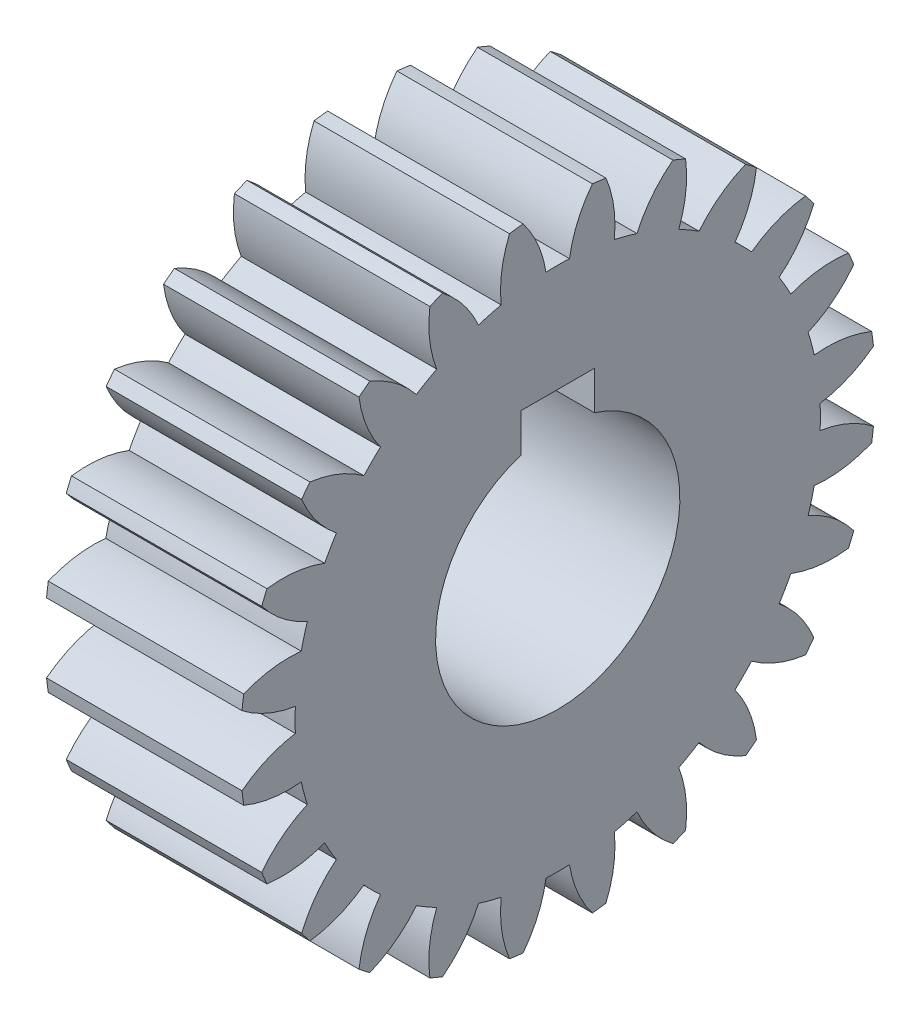
SolidWorks part; units mm, degrees
ref_plane "Plane1" through (0, 0, 0) normal (0, 0, 1) x (1, 0, 0)
ref_plane "Plane2" through (0, 0, 0) normal (0, 1, 0) x (1, 0, 0)
ref_plane "Plane3" through (0, 0, 0) normal (1, 0, 0) x (0, 0, -1)
sketch "HoldingSke" plane through (0, 0, 0) normal (0, 1, 0) x (1, 0, 0)
  line L0 (0, 0) -> (371.2649, -165.2978)
  line L1 (-15, 0) -> (100, 0) construction
  line L2 (0, 0) -> (-2.1039, 2.3779)
  line L3 (0, 0) -> (-11.863, 4.5341)
  line L4 (0, 0) -> (7.8894, 3.5126)
  line L5 (0, 0) -> (-47.5972, -17.7524)
  line L6 (0, 0) -> (-10.5278, -7.1032)
  line L7 (-2.1039, 2.3779) -> (8.8308, 51.9871)
  line L8 (-76.2, 54.61) -> (-58.9788, 54.61)
  line L9 (-71.009, 38.7566) -> (-53.1078, 45.2721)
  line L10 (-76.2, 71.12) -> (104.1128, 71.12)
  line L11 (0, 0) -> (-12.7, 0)
  line L12 (-76.2, 101.6) -> (-76.1428, 101.6)
  line L13 (24.9733, 27.94) -> (52.9518, 28.4284)
  line L14 (24.9733, 27.94) -> (24.9746, 27.94)
  line L15 (24.9733, 27.94) -> (100.4006, 29.5858)
  circle A0 centre (0, 0) radius 7.9375
  circle A1 centre (0, 0) radius 17.0644
  circle A2 centre (0, 0) radius 38.1
  circle A3 centre (0, 0) radius 7.9375
  dimension "MHD" = 34.1287
  dimension "Hub_dia" = 76.2
  dimension "Bore" = 15.875
  dimension "MBD" = 15.875
  dimension "Num_teeth" = 24
  dimension "Pitch" = 406.4
  dimension "Overall_len" = 50.8
  dimension "Show_teeth" = 24
  dimension "Thickness" = 12.7
  dimension "OAL" = 50.8001
  dimension "T_dim" = 17.2212
  dimension "Ap" = 20
  dimension "H" = 19.05
  dimension "Pitch_radius" = 180.3128
  dimension "Width" = 12.7
  dimension "Backlash" = 0.0571
  dimension "Addendum_fac" = 1
  dimension "Dedendum_fac" = 1.25
  dimension "Clearance_fac" = 0.25
  dimension "Dedendum_add" = 0.0013
sketch "BasProSke" plane through (0, 0, 0) normal (0, 1, 0) x (1, 0, 0)
  line L0 (-10, 0) -> (60, 0) construction
  line L1 (0, 0) -> (0, 20.6375)
  line L2 (0, 0) -> (12.7, 0)
  line L3 (12.7, 0) -> (12.7, 20.6375)
  line L4 (12.7, 20.6375) -> (0, 20.6375)
  dimension "Thickness" = 12.7
  dimension "Diameter" = 41.275
revolve "Base-Revolve" add sketch "BasProSke" angle 360 about L0
sketch "TooCutSke" plane through (0, 0, 0) normal (1, 0, 0) x (0, 0, -1)
  line L1 (0, 0) -> (0, 107) construction
  line L2 (0, 0) -> (-1.3459, 19.0024) construction
  line L3 (0, 0) -> (-4.964, 37.7056) construction
  line L4 (-1.3459, 19.0024) -> (-2.482, 18.8528) construction
  arc A0 (0.7625, 17.0473) -> (-0.7625, 17.0473) centre (0, 0) ccw
  arc A1 (2.2707, 20.5378) -> (-2.2707, 20.5378) centre (0, 0) ccw
  circle A2 centre (0, 0) radius 19.05 construction
  circle A3 centre (0, 0) radius 17.9011 construction
  arc A4 (-0.7625, 17.0473) -> (-2.2707, 20.5378) centre (-8.2904, 15.8657) ccw
  arc A5 (2.2707, 20.5378) -> (0.7625, 17.0473) centre (8.2904, 15.8657) ccw
  dimension "Root_dia" = 34.1287
  dimension "Overcut_dia" = 41.3258
  dimension "Pitch_dia" = 38.1
  dimension "Base_dia" = 35.8023
  dimension "Flank_rad" = 7.62
  dimension "Half_ang" = 7.5
  dimension "Half_CT" = 1.1459
extrude "ToothCut" cut sketch "TooCutSke" along normal through all
fillet "Breaks" [suppressed] radius 0.0318
fillet "RootFillets" [suppressed] radius 0.3981
pattern_circular "TeethCuts" count 24 every 15 about axis through (-10, 0, 0) along (1, 0, 0) of "ToothCut", "RootFillets", "Breaks"
sketch "HubNeaOneSke" plane through (0, 0, 0) normal (-1, 0, 0) x (0, 0, 1)
  circle A0 centre (0, 0) radius 17.0644
  dimension "Diameter" = 34.1287
extrude "HubNearOne" [suppressed] add sketch "HubNeaOneSke" along normal blind 38.1001
sketch "HubNeaBotSke" plane through (0, 0, 0) normal (-1, 0, 0) x (0, 0, 1)
  circle A0 centre (0, 0) radius 17.0644
  dimension "Diameter" = 34.1287
extrude "HubNearBoth" [suppressed] add sketch "HubNeaBotSke" along normal blind 19.05
ref_plane "FarPln" through (12.7, 0, 0) normal (1, 0, 0) x (0, 0, -1)
sketch "HubFarSke" plane through (12.7, 0, 0) normal (1, 0, 0) x (0, 0, -1)
  circle A0 centre (0, 0) radius 17.0644
  dimension "Diameter" = 34.1287
extrude "HubFar" [suppressed] add sketch "HubFarSke" along normal blind 19.05
sketch "BorSke" plane through (0, 0, 0) normal (1, 0, 0) x (0, 0, -1)
  circle A0 centre (0, 0) radius 7.9375
  dimension "Diameter" = 15.875
extrude "Bore" cut sketch "BorSke" along normal mid plane 101.6001
sketch "KeySke" plane through (0, 0, 0) normal (1, 0, 0) x (0, 0, -1)
  line L0 (-2.3813, 0) -> (-2.3813, 9.2837)
  line L1 (-2.3813, 9.2837) -> (2.3813, 9.2837)
  line L2 (2.3813, 9.2837) -> (2.3813, 0)
  line L3 (0, 0) -> (0, 34) construction
  line L4 (-2.3813, 0) -> (2.3813, 0)
  dimension "Offset" = 9.2837
  dimension "Width" = 4.7625
extrude "Keyway" cut sketch "KeySke" along normal mid plane 101.6001
pattern_circular "Keyway2" [suppressed] count 2 every 90 about axis through (-10, 0, 0) along (1, 0, 0)
sketch "Sketch2" plane through (12.7, 0, 0) normal (1, 0, 0) x (0, 0, -1)
  line L3 (-2.3813, 9.2837) -> (-2.3813, 10.0711)
  line L4 (2.3813, 9.2837) -> (2.3813, 10.0711)
  line L5 (-2.3813, 10.0711) -> (2.3813, 10.0711)
extrude "Cut-Extrude2" cut sketch "Sketch2" against normal through all
equation "' \"Pitch@HoldingSke\" = 4"
equation "' \"Num_teeth@HoldingSke\" = 12"
equation "' \"Ap@HoldingSke\" =  20"
equation "' \"Ap@HoldingSke\" = 20"
equation "' \"Width@HoldingSke\" = 0.5"
equation "' \"Hub_dia@HoldingSke\"= 1"
equation "' \"Hub_dia@HoldingSke\" = 1"
equation "' \"Overall_len@HoldingSke\" = 1.0"
equation "' \"Bore@HoldingSke\" = 0.75"
equation "' \"T_dim@HoldingSke\" = 0.85"
equation "' \"Width@KeySke\" = 0.25"
equation "' \"Show_teeth@HoldingSke\" = 13"
equation "' \"Backlash@HoldingSke\" = 0.009"
equation "' \"Addendum_fac@HoldingSke\" = 1.0"
equation "' \"Dedendum_fac@HoldingSke\" = 1.25"
equation "' \"Dedendum_add@HoldingSke\" = 0.00005"
equation "' \"Clearance_fac@HoldingSke\" = 0.25"
equation "' \"Pitch@HoldingSke\" = 0.5"
equation "' \"Num_teeth@HoldingSke\" = 23"
equation "' \"Show_teeth@HoldingSke\" = 23"
equation "' \"Backlash@HoldingSke\" = 0.0375"
equation "\"Overcut_dia@TooCutSke\" = (\"Num_teeth@HoldingSke\" + 2 * \"Addendum_fac@HoldingSke\") / \"Pitch@HoldingSke\" + 0.002"
equation "\"Pitch_dia@TooCutSke\" = \"Num_teeth@HoldingSke\" / \"Pitch@HoldingSke\""
equation "\"Base_dia@TooCutSke\" = \"Num_teeth@HoldingSke\" / \"Pitch@HoldingSke\" * cos((\"Ap@HoldingSke\"  * 3.14159265 / 180))"
equation "\"Root_dia@TooCutSke\" = (\"Num_teeth@HoldingSke\" + 2) / \"Pitch@HoldingSke\" - 2 * (\"Addendum_fac@HoldingSke\" + \"Dedendum_fac@HoldingSke\") / \"Pitch@HoldingSke\" - \"Dedendum_add@HoldingSke\" * 2"
equation "\"Half_ang@TooCutSke\" = 180 / \"Num_teeth@HoldingSke\""
equation "\"Half_CT@TooCutSke\" = \"Num_teeth@HoldingSke\" / \"Pitch@HoldingSke\" * sin((3.14159265 / 2 / \"Num_teeth@HoldingSke\")) / 2 - 7 * \"Backlash@HoldingSke\" / 4"
equation "\"Flank_rad@TooCutSke\" = \"Num_teeth@HoldingSke\" / \"Pitch@HoldingSke\" / 5"
equation "\"Radius@RootFillets\" = \"Clearance_fac@HoldingSke\" / \"Pitch@HoldingSke\" + \"Dedendum_add@HoldingSke\""
equation "\"Break_rad@Breaks\" = 0.02 / \"Pitch@HoldingSke\""
equation "\"Thickness@HoldingSke\" = \"Width@HoldingSke\""
equation "\"OAL@HoldingSke\" = \"Thickness@HoldingSke\""
equation "\"MHD@HoldingSke\" = (\"Num_teeth@HoldingSke\" + 2) / \"Pitch@HoldingSke\" - 2 * (\"Addendum_fac@HoldingSke\" + \"Dedendum_fac@HoldingSke\")  / \"Pitch@HoldingSke\" - \"Dedendum_add@HoldingSke\" * 2"
equation "\"MBD@HoldingSke\" = (\"Num_teeth@HoldingSke\" + 2) / \"Pitch@HoldingSke\" - 2 * (\"Addendum_fac@HoldingSke\" + \"Dedendum_fac@HoldingSke\")  / \"Pitch@HoldingSke\" - \"Dedendum_add@HoldingSke\" * 2 - 0.002"
equation "\"MHD@HoldingSke\" = ((sgn( \"MHD@HoldingSke\" - \"Hub_dia@HoldingSke\" )-1)*( \"MHD@HoldingSke\" - \"Hub_dia@HoldingSke\" ))/-2+ \"Hub_dia@HoldingSke\""
equation "\"MBD@HoldingSke\" = ((sgn( \"MBD@HoldingSke\" - \"Bore@HoldingSke\" )-1)*( \"MBD@HoldingSke\" - \"Bore@HoldingSke\" ))/-2+ \"Bore@HoldingSke\""
equation "\"OAL@HoldingSke\" = ((sgn( \"OAL@HoldingSke\" - \"Overall_len@HoldingSke\" )+1)*( \"OAL@HoldingSke\" - \"Overall_len@HoldingSke\" ))/2 + \"Overall_len@HoldingSke\" + 0.000002"
equation "\"Num_teeth@TeethCuts\" = int( \"Show_teeth@HoldingSke\" ) + 1"
equation "\"Num_teeth@TeethCuts\" = ((sgn( \"Num_teeth@TeethCuts\" - \"Num_teeth@HoldingSke\" )-1)*( \"Num_teeth@TeethCuts\" - \"Num_teeth@HoldingSke\" ))/-2+ \"Num_teeth@HoldingSke\""
equation "\"Num_teeth@TeethCuts\" = ((sgn( \"Num_teeth@TeethCuts\" - 2.0)+1)*( \"Num_teeth@TeethCuts\" - 2.0))/2 +2.0"
equation "\"Angle@TeethCuts\" = 360.0 / \"Num_teeth@HoldingSke\""
equation "\"Diameter@BasProSke\" = (\"Num_teeth@HoldingSke\" + 2 * \"Addendum_fac@HoldingSke\") / \"Pitch@HoldingSke\""
equation "\"Thickness@BasProSke\"  = \"Thickness@HoldingSke\""
equation "' \"Fillet_rad@BasProSke\" =  \"Thickness@HoldingSke\" * 0.05"
equation "' \"Fillet_rad@BasProSke\" = \"Thickness@HoldingSke\" * 0.05"
equation "\"MHD@HoldingSke\" = ((sgn( \"MHD@HoldingSke\" - \"Root_dia@TooCutSke\" )-1)*( \"MHD@HoldingSke\" - \"Root_dia@TooCutSke\" ))/-2+ \"Root_dia@TooCutSke\""
equation "\"Diameter@HubNeaOneSke\" = \"MHD@HoldingSke\""
equation "\"Length@HubNearOne\" = \"OAL@HoldingSke\" - \"Thickness@BasProSke\""
equation "\"Diameter@HubNeaBotSke\" = \"MHD@HoldingSke\""
equation "\"Length@HubNearBoth\" = ( \"OAL@HoldingSke\" - \"Thickness@BasProSke\" ) / 2.0"
equation "\"Thickness@FarPln\" = \"Thickness@BasProSke\""
equation "\"Diameter@HubFarSke\" = \"MHD@HoldingSke\""
equation "\"Length@HubFar\" = ( \"OAL@HoldingSke\" - \"Thickness@BasProSke\" ) / 2.0"
equation "\"Diameter@BorSke\" = \"MBD@HoldingSke\""
equation "\"D1@Bore\" = \"OAL@HoldingSke\" * 2.0"
equation "\"D1@Keyway\" = \"OAL@HoldingSke\" * 2.0"
equation "\"Offset@KeySke\" = \"T_dim@HoldingSke\" - \"MBD@HoldingSke\" / 2.0"
